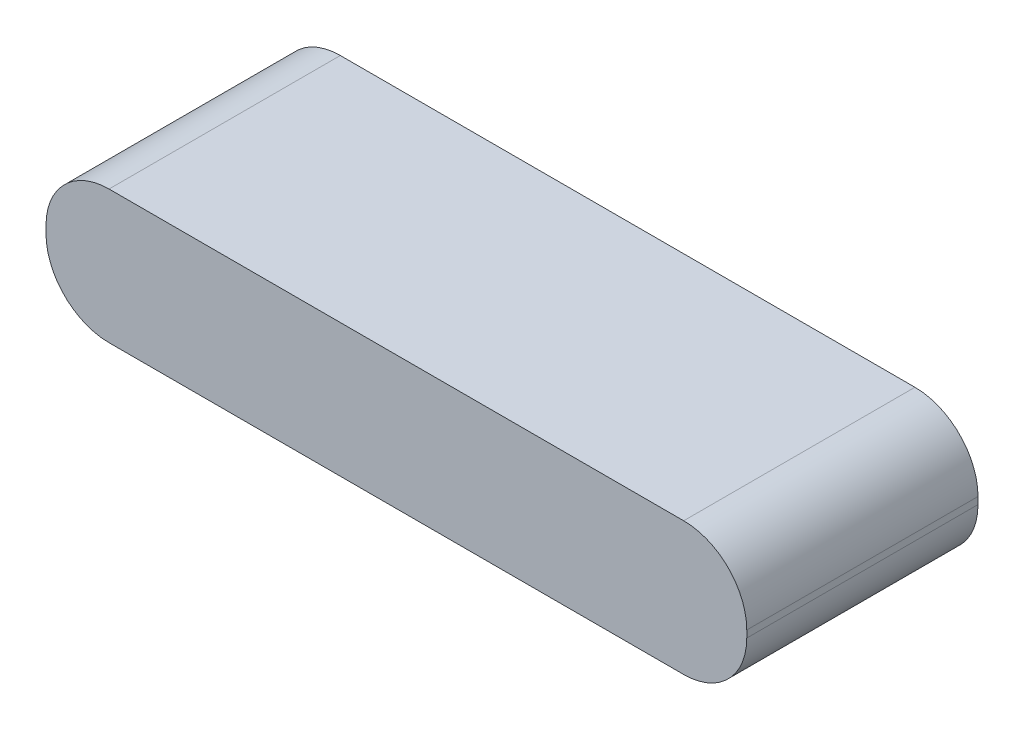
SolidWorks part; units mm, degrees
ref_plane "Front" through (0, 0, 0) normal (0, 0, 1) x (1, 0, 0)
ref_plane "Top" through (0, 0, 0) normal (0, 1, 0) x (1, 0, 0)
ref_plane "Right" through (0, 0, 0) normal (1, 0, 0) x (0, 0, -1)
sketch "Sketch1" plane through (0, 0, 0) normal (0, 1, 0) x (1, 0, 0)
  line L1 (-50, 16.5) -> (50, 16.5)
  line L2 (-50, 16.5) -> (-50, -16.5)
  line L3 (-50, -16.5) -> (50, -16.5)
  line L4 (50, 16.5) -> (50, -16.5)
  line L5 (-50, 16.5) -> (50, -16.5) construction
  line L6 (-50, -16.5) -> (50, 16.5) construction
  point P0 (0, 0)
  dimension "D1" = 100
  dimension "D2" = 33
extrude "Boss-Extrude1" add sketch "Sketch1" along normal blind 19
fillet "Fillet1" radius 9 4 edges at (-50, 0, 0) (-50, 19, 0) (50, 0, 0) (50, 19, 0)
